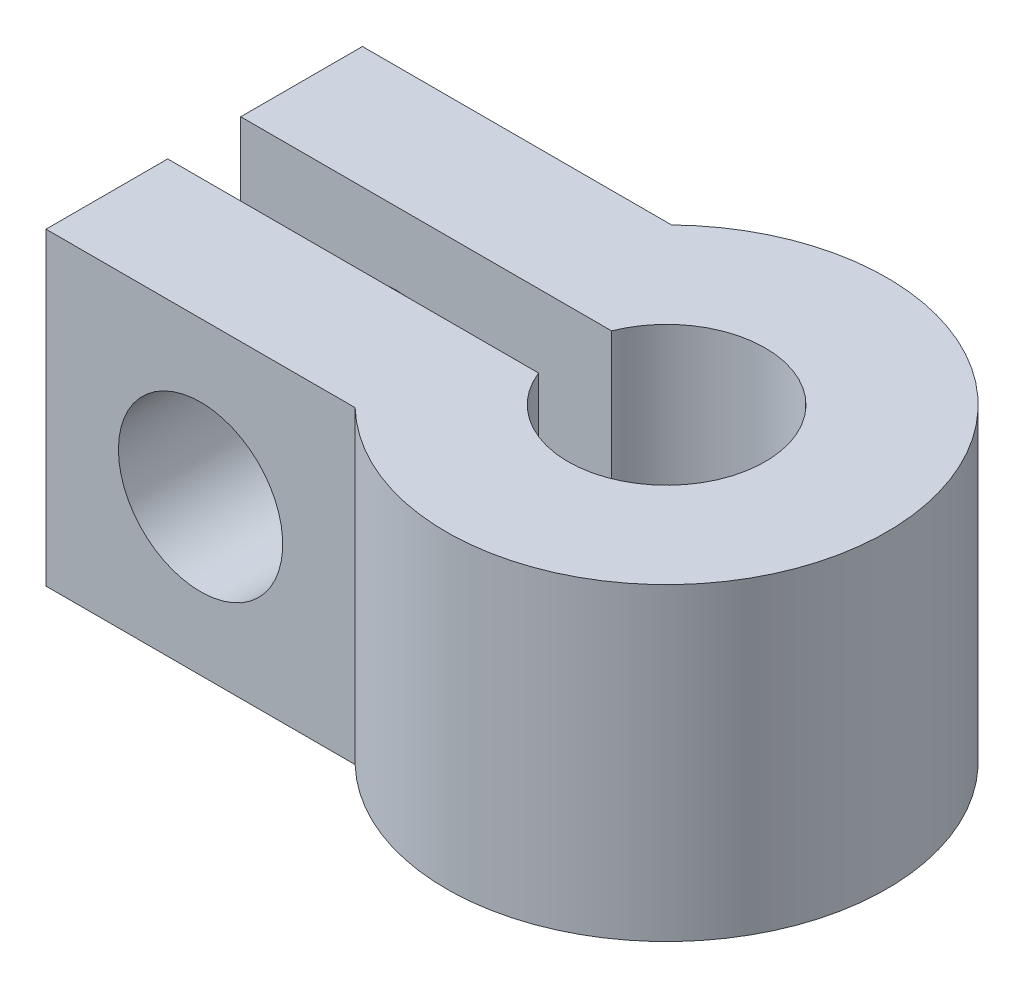
SolidWorks part; units mm, degrees
ref_plane "Front Plane" through (0, 0, 0) normal (0, 0, 1) x (1, 0, 0)
ref_plane "Top Plane" through (0, 0, 0) normal (0, 1, 0) x (1, 0, 0)
ref_plane "Right Plane" through (0, 0, 0) normal (1, 0, 0) x (0, 0, -1)
sketch "Sketch1" plane through (0, 0, 0) normal (0, 1, 0) x (1, 0, 0)
  line L0 (-3.762, 1.5) -> (-18.997, 1.5)
  line L1 (-18.997, 1.5) -> (-18.997, 6.5)
  line L2 (-18.997, 6.5) -> (-6.297, 6.5)
  line L3 (-3.762, -1.5) -> (-18.997, -1.5)
  line L4 (-18.997, -1.5) -> (-18.997, -6.5)
  line L5 (-18.997, -6.5) -> (-6.297, -6.5)
  circle A0 centre (0, 0) radius 4.05
  arc A2 (-6.297, 6.5) -> (-6.297, -6.5) centre (0, 0) cw
  point P11 (-3.8869, -0.7032)
  point P12 (-3.7134, 1.3466)
  point P13 (-3.6752, -1.4475)
  dimension "D1" = 5
  dimension "D2" = 8.1
  dimension "D3" = 12.7
  dimension "D4" = 5
  dimension "D5" = 3
extrude "Boss-Extrude1" add sketch "Sketch1" along normal blind 12.7 contours A2 L2 L1 L0 A0 L3 L4 L5
sketch "Sketch2" plane through (0, 0, -6.5) normal (0, 0, -1) x (-1, 0, 0)
  line L0 (12.647, 12.7) -> (12.647, 0) construction
  line L1 (18.997, 12.7) -> (6.297, 12.7) construction
  line L2 (18.997, 0) -> (6.297, 0) construction
  circle A0 centre (12.647, 6.35) radius 3.375
  dimension "D1" = 6.75
extrude "Cut-Extrude1" cut sketch "Sketch2" against normal through all
